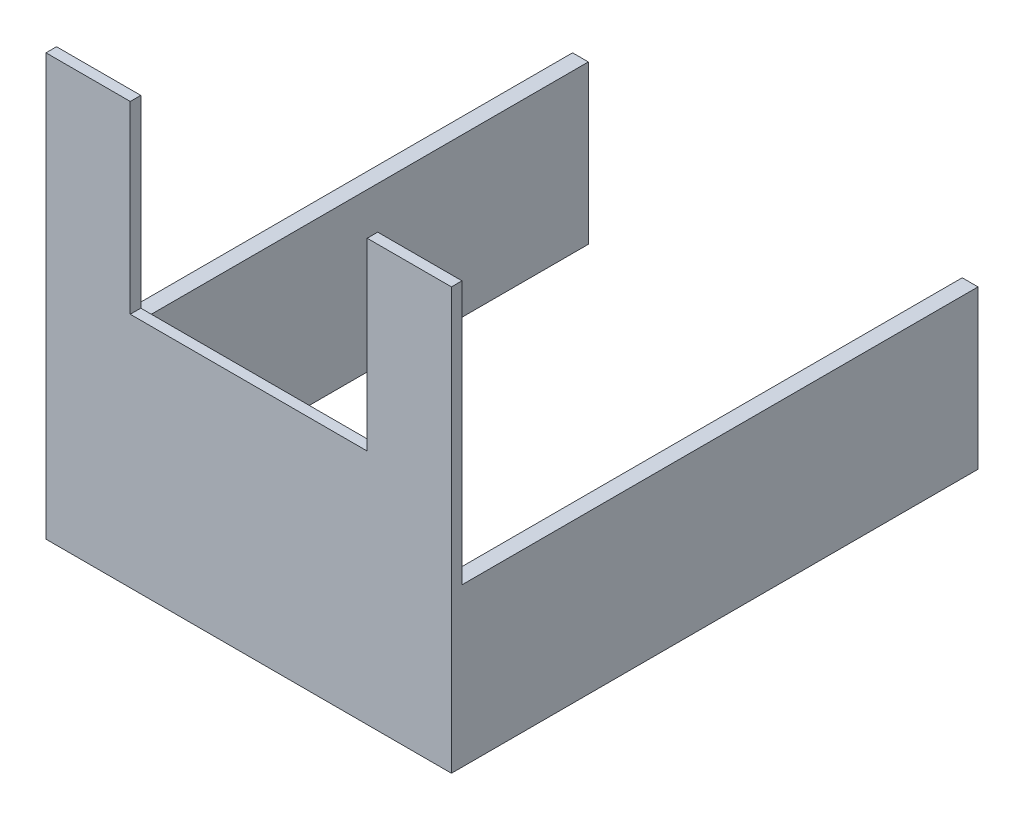
SolidWorks part; units mm, degrees
ref_plane "前视基准面" through (0, 0, 0) normal (0, 0, 1) x (1, 0, 0)
ref_plane "上视基准面" through (0, 0, 0) normal (0, 1, 0) x (1, 0, 0)
ref_plane "右视基准面" through (0, 0, 0) normal (1, 0, 0) x (0, 0, -1)
other "Configuration Table"
sketch "草图1" plane through (0, 0, 0) normal (0, 0, 1) x (1, 0, 0)
  line L1 (-22.8345, 16.7276) -> (54.1655, 16.7276)
  line L2 (-22.8345, 16.7276) -> (-22.8345, -63.2724)
  line L3 (-22.8345, -63.2724) -> (54.1655, -63.2724)
  line L4 (54.1655, 16.7276) -> (54.1655, -63.2724)
  dimension "D1" = 77
  dimension "D2" = 80
extrude "凸台-拉伸1" add sketch "草图1" along normal blind 100
sketch "草图2" plane through (0, 0, 100) normal (0, 0, 1) x (1, 0, 0)
  line L0 (54.1655, 16.7276) -> (-22.8345, 16.7276) construction
  line L1 (-6.8345, 16.7276) -> (38.1655, 16.7276)
  line L2 (-6.8345, 16.7276) -> (-6.8345, -18.2724)
  line L3 (-6.8345, -18.2724) -> (38.1655, -18.2724)
  line L4 (38.1655, 16.7276) -> (38.1655, -18.2724)
  point P4 (15.6655, 16.7276)
  dimension "D1" = 45
  dimension "D2" = 35
extrude "切除-拉伸1" cut sketch "草图2" against normal blind 100
sketch "草图3" plane through (0, 0, 0) normal (0, 0, -1) x (-1, 0, 0)
  line L0 (-54.1655, 16.7276) -> (-38.1655, 16.7276) construction
  line L1 (-51.1655, 16.7276) -> (19.8345, 16.7276)
  line L2 (-51.1655, 16.7276) -> (-51.1655, -63.2724)
  line L3 (-51.1655, -63.2724) -> (19.8345, -63.2724)
  line L4 (19.8345, 16.7276) -> (19.8345, -63.2724)
  line L5 (22.8345, 16.7276) -> (22.8345, -63.2724) construction
  line L6 (-54.1655, -63.2724) -> (-54.1655, 16.7276) construction
  line L7 (22.8345, -63.2724) -> (-54.1655, -63.2724) construction
  dimension "D1" = 3
  dimension "D2" = 3
  dimension "D3" = 0
extrude "切除-拉伸2" cut sketch "草图3" against normal blind 98
sketch "草图5" plane through (-22.8345, 0, 0) normal (-1, 0, 0) x (0, 0, 1)
  line L0 (100, 16.7276) -> (100, -63.2724) construction
  line L1 (0, 16.7276) -> (98, 16.7276)
  line L2 (0, 16.7276) -> (0, -33.2724)
  line L3 (0, -33.2724) -> (98, -33.2724)
  line L4 (98, 16.7276) -> (98, -33.2724)
  line L5 (100, -63.2724) -> (0, -63.2724) construction
  dimension "D1" = 2
  dimension "D2" = 30
extrude "切除-拉伸3" cut sketch "草图5" against normal blind 98
